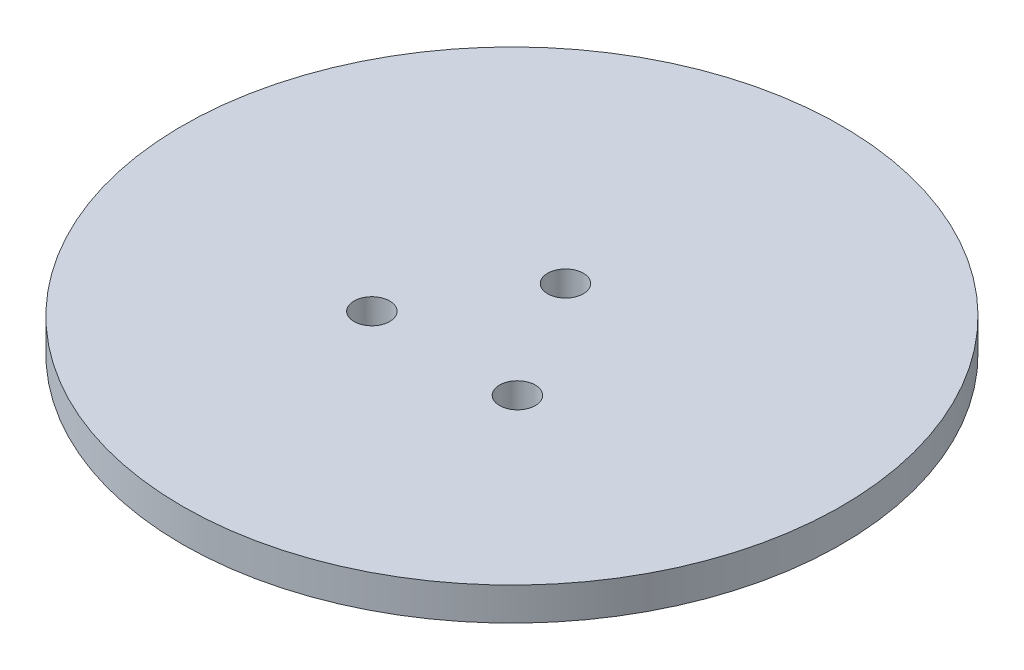
SolidWorks part; units mm, degrees
ref_plane "Front Plane" through (0, 0, 0) normal (0, 0, 1) x (1, 0, 0)
ref_plane "Top Plane" through (0, 0, 0) normal (0, 1, 0) x (1, 0, 0)
ref_plane "Right Plane" through (0, 0, 0) normal (1, 0, 0) x (0, 0, -1)
sketch "Sketch1" plane through (0, 0, 0) normal (0, 1, 0) x (1, 0, 0)
  line L0 (-59.1648, -12.192) -> (66.8918, -12.192) construction
  circle A0 centre (0, 0) radius 60.96
  circle A1 centre (-0.254, 10.16) radius 3.302
  circle A2 centre (-13.716, -12.192) radius 3.302
  circle A3 centre (13.208, -12.192) radius 3.302
  circle A4 centre (0, 0) radius 13.335 construction
  dimension "D1" = 121.92
  dimension "D2" = 6.604
  dimension "D3" = 6.604
  dimension "D4" = 6.604
  dimension "D5" = 26.67
  dimension "D6" = 13.716
  dimension "D9" = 10.16
  dimension "D10" = 12.192
  dimension "D11" = 0.254
  dimension "D8" = 13.208
extrude "Extrude1" add sketch "Sketch1" along normal blind 6.096
sketch "Sketch2" plane through (0, 0, 0) normal (0, -1, 0) x (1, 0, 0)
  circle A0 centre (13.208, 12.192) radius 3.302
  circle A1 centre (-0.254, -10.16) radius 3.302
  circle A2 centre (-13.716, 12.192) radius 3.302
extrude "Boss-Extrude1" add sketch "Sketch2" along normal blind 25.4 separate body
sketch "Sketch3" plane through (0, -25.4, 0) normal (0, -1, 0) x (1, 0, 0)
  circle A0 centre (-0.254, -10.16) radius 1.27
  circle A1 centre (13.208, 12.192) radius 1.27
  circle A2 centre (-13.716, 12.192) radius 1.27
  dimension "D1" = 2.54
  dimension "D2" = 2.54
  dimension "D3" = 2.54
extrude "Cut-Extrude1" cut sketch "Sketch3" against normal through all
equation "\"MATERIAL\"=0.24"
equation "\"D1@Extrude1\" = \"MATERIAL\""
equation "\"mountingHole\"= .26"
equation "\"D2@Sketch1\" = \"mountingHole\""
equation "\"D3@Sketch1\" = \"mountingHole\""
equation "\"D4@Sketch1\" = \"mountingHole\""
